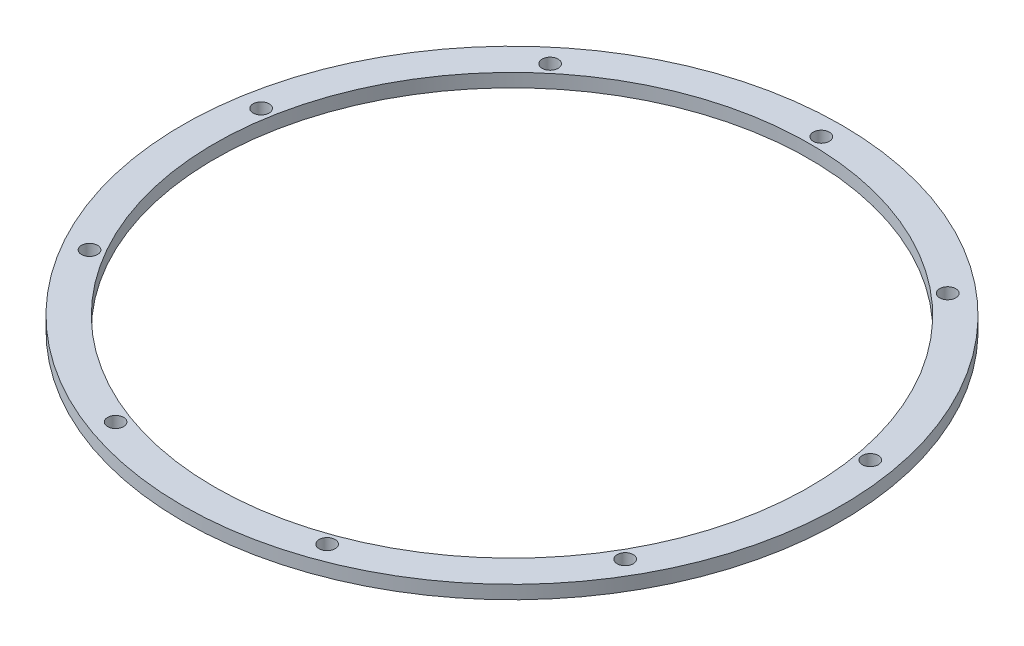
SolidWorks part; units mm, degrees
material "Acier non allié"
ref_plane "Plan de face" through (0, 0, 0) normal (0, 0, 1) x (1, 0, 0)
ref_plane "Plan de dessus" through (0, 0, 0) normal (0, 1, 0) x (1, 0, 0)
ref_plane "Plan de droite" through (0, 0, 0) normal (1, 0, 0) x (0, 0, -1)
sketch "Esquisse1" plane through (0, 0, 0) normal (0, 1, 0) x (1, 0, 0)
  circle A0 centre (0, 0) radius 111.1
  circle A1 centre (0, 0) radius 123.075
  circle A2 centre (0, 115.5) radius 3
  circle A3 centre (74.242, 88.4781) radius 3
  circle A4 centre (113.7453, 20.0564) radius 3
  circle A5 centre (100.0259, -57.75) radius 3
  circle A6 centre (39.5033, -108.5345) radius 3
  circle A7 centre (-39.5033, -108.5345) radius 3
  circle A8 centre (-100.0259, -57.75) radius 3
  circle A9 centre (-113.7453, 20.0564) radius 3
  circle A10 centre (-74.242, 88.4781) radius 3
  point P24 (0, 0)
  dimension "D1" = 222.2
  dimension "D2" = 246.15
  dimension "D3" = 115.5
  dimension "D4" = 9
extrude "Boss.-Extru.1" add sketch "Esquisse1" along normal blind 5
